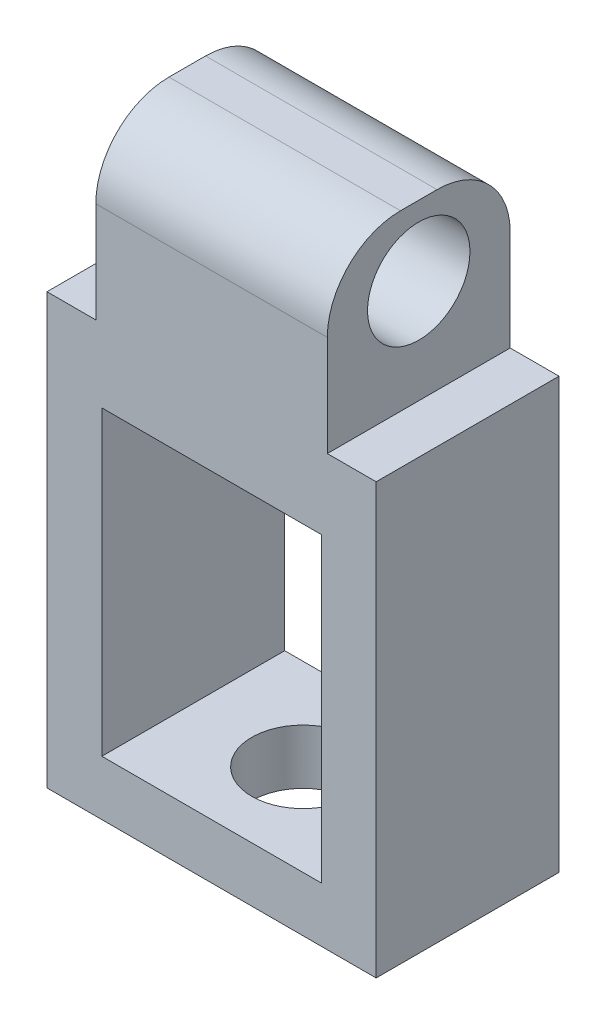
SolidWorks part; units mm, degrees
ref_plane "Front Plane" through (0, 0, 0) normal (0, 0, 1) x (1, 0, 0)
ref_plane "Top Plane" through (0, 0, 0) normal (0, 1, 0) x (1, 0, 0)
ref_plane "Right Plane" through (0, 0, 0) normal (1, 0, 0) x (0, 0, -1)
sketch "Sketch1" plane through (0, 0, 0) normal (0, 0, 1) x (1, 0, 0)
  line L0 (-12.3631, 11.2393) -> (-6.0331, 11.2393)
  line L1 (-6.0331, 11.2393) -> (-6.0331, 6.4893)
  line L2 (-6.0331, 6.4893) -> (-4.6981, 6.4893)
  line L3 (-4.6981, 6.4893) -> (-4.6981, -5.2607)
  line L4 (-4.6981, -5.2607) -> (-13.6981, -5.2607)
  line L5 (-13.6981, -5.2607) -> (-13.6981, 6.4893)
  line L6 (-13.6981, 6.4893) -> (-12.3631, 6.4893)
  line L7 (-12.3631, 6.4893) -> (-12.3631, 11.2393)
  line L8 (-9.1981, 4.4893) -> (-6.1981, 4.4893)
  line L9 (-9.1981, 4.4893) -> (-12.1981, 4.4893)
  line L10 (-12.1981, 4.4893) -> (-12.1981, -3.7607)
  line L11 (-12.1981, -3.7607) -> (-6.1981, -3.7607)
  line L12 (-6.1981, -3.7607) -> (-6.1981, 4.4893)
  line L13 (-9.1981, 11.2393) -> (-9.1981, 4.4893) construction
  dimension "D1" = 6.33
  dimension "D2" = 3
  dimension "D3" = 3
  dimension "D4" = 8.25
  dimension "D5" = 1.5
  dimension "D6" = 1.5
  dimension "D7" = 1.5
  dimension "D8" = 2
  dimension "D9" = 4.75
extrude "Boss-Extrude1" add sketch "Sketch1" along normal blind 5
sketch "Sketch2" plane through (-6.0331, 0, 0) normal (1, 0, 0) x (0, 0, -1)
  line L0 (-2.5, 11.2393) -> (-2.5, 6.4893) construction
  line L1 (-5, 11.2393) -> (0, 11.2393) construction
  line L2 (-5, 6.4893) -> (0, 6.4893) construction
  line L3 (-5, 9.3235) -> (0, 9.3235) construction
  line L4 (-5, 6.4893) -> (-5, 11.2393) construction
  line L5 (0, 6.4893) -> (0, 11.2393) construction
  circle A0 centre (-2.5, 9.3235) radius 1.4
  dimension "D1" = 2.8
extrude "Cut-Extrude1" cut sketch "Sketch2" against normal blind 8
sketch "Sketch3" plane through (0, -5.2607, 0) normal (0, -1, 0) x (1, 0, 0)
  line L0 (-9.1981, 5) -> (-9.1981, 0) construction
  line L1 (-13.6981, 5) -> (-4.6981, 5) construction
  line L2 (-13.6981, 0) -> (-4.6981, 0) construction
  line L3 (-13.6981, 2.5) -> (-4.6981, 2.5) construction
  line L4 (-13.6981, 5) -> (-13.6981, 0) construction
  line L5 (-4.6981, 5) -> (-4.6981, 0) construction
  circle A0 centre (-9.1981, 2.5) radius 1.4
  dimension "D1" = 2.8
extrude "Cut-Extrude2" cut sketch "Sketch3" against normal blind 6
fillet "Fillet1" radius 2 2 edges at (-9.1981, 11.2393, 0) (-9.1981, 11.2393, 5)
